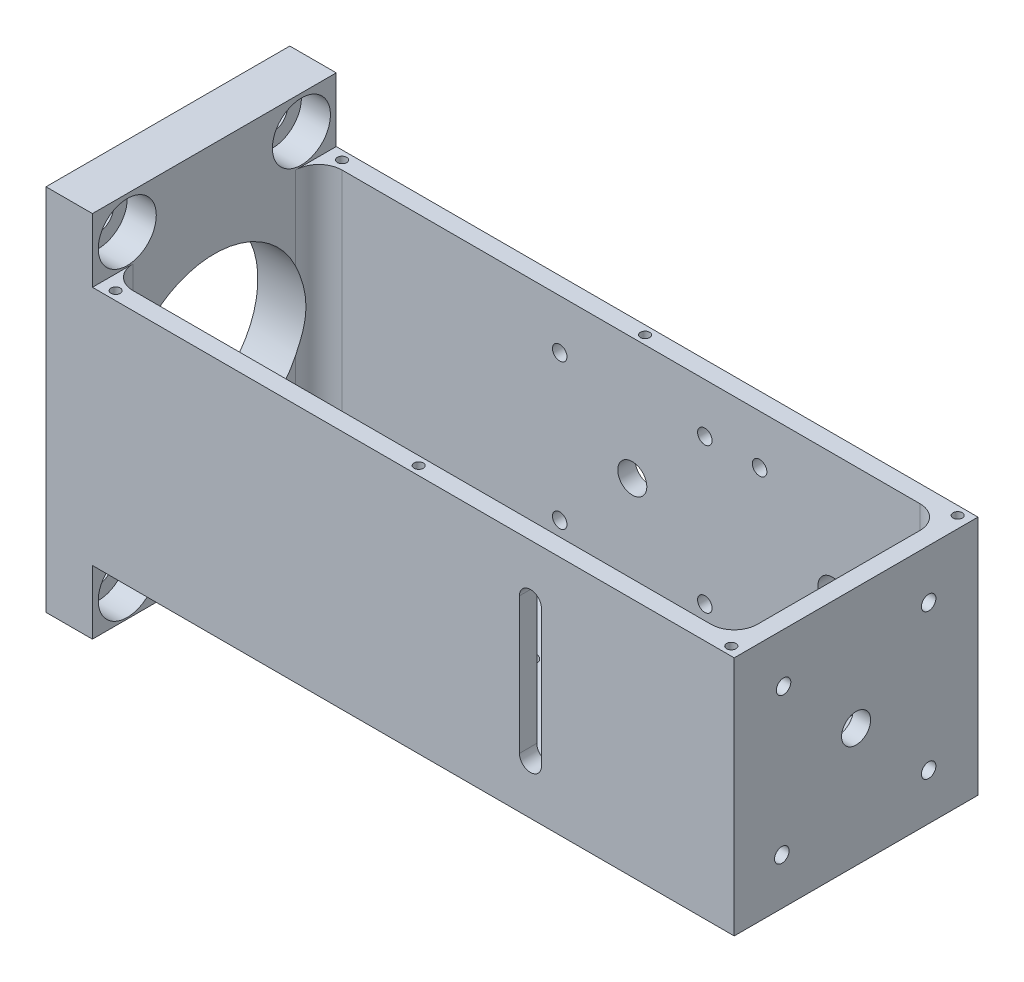
SolidWorks part; units mm, degrees
material "6061-T6 (SS)"
ref_plane "Front Plane" through (0, 0, 0) normal (0, 0, 1) x (1, 0, 0)
ref_plane "Top Plane" through (0, 0, 0) normal (0, 1, 0) x (1, 0, 0)
ref_plane "Right Plane" through (0, 0, 0) normal (1, 0, 0) x (0, 0, -1)
sketch "Sketch1" plane through (0, 0, 0) normal (0, 1, 0) x (1, 0, 0)
  line L1 (-59.28, -21) -> (59.28, -21)
  line L2 (-59.28, -21) -> (-59.28, 21)
  line L3 (-59.28, 21) -> (59.28, 21)
  line L4 (59.28, -21) -> (59.28, 21)
  line L5 (-59.28, -21) -> (59.28, 21) construction
  line L6 (-59.28, 21) -> (59.28, -21) construction
  point P0 (0, 0)
  dimension "D1" = 118.56
  dimension "D2" = 42
extrude "Boss-Extrude1" add sketch "Sketch1" along normal blind 41.5
sketch "Sketch2" plane through (0, 41.5, 0) normal (0, 1, 0) x (1, 0, 0)
  line L0 (59.28, -21) -> (59.28, 21) construction
  line L1 (56.28, -18) -> (-51.28, -18)
  line L2 (56.28, -18) -> (56.28, 18)
  line L3 (56.28, 18) -> (-51.28, 18)
  line L4 (-51.28, -18) -> (-51.28, 18)
  line L5 (-59.28, -21) -> (59.28, -21) construction
  line L6 (59.28, 21) -> (-59.28, 21) construction
  line L7 (-59.28, 21) -> (-59.28, -21) construction
  point P0 (0, 0)
  dimension "D1" = 3
  dimension "D2" = 3
  dimension "D3" = 3
  dimension "D4" = 8
extrude "Cut-Extrude1" cut sketch "Sketch2" against normal blind 37.5
fillet "Fillet1" radius 4 4 edges at (56.28, 22.75, -18) (-51.28, 22.75, -18) (56.28, 22.75, 18) (-51.28, 22.75, 18)
sketch "Sketch3" plane through (-59.28, 0, 0) normal (-1, 0, 0) x (0, 0, 1)
  line L0 (-21, 0) -> (21, 0) construction
  line L1 (21, 41.5) -> (21, 0) construction
  circle A0 centre (0, 20.5) radius 15.5
  dimension "D1" = 31
  dimension "D2" = 20.5
  dimension "D3" = 21
extrude "Cut-Extrude2" cut sketch "Sketch3" against normal up to next
sketch "Sketch10" plane through (0, 0, 21) normal (0, 0, 1) x (1, 0, 0)
  line L0 (24.18, 8.0181) -> (24.18, 32.9819) construction
  line L1 (-59.28, 0) -> (59.28, 0) construction
  line L3 (26.08, 32.25) -> (26.08, 8.75)
  line L5 (22.28, 32.25) -> (22.28, 8.75)
  line L8 (59.28, 41.5) -> (59.28, 0) construction
  arc A0 (22.28, 8.75) -> (26.08, 8.75) centre (24.18, 8.75) ccw
  arc A1 (26.08, 32.25) -> (22.28, 32.25) centre (24.18, 32.25) ccw
  point P2 (24.18, 20.5)
  dimension "D2" = 3.8
  dimension "D1" = 8.75
  dimension "D4" = 35.1
  dimension "D7" = 23.5
extrude "Cut-Extrude5" cut sketch "Sketch10" against normal up to next
sketch "Sketch22" plane through (0, 0, 0) normal (0, -1, 0) x (1, 0, 0)
  line L0 (59.28, -21) -> (-59.28, -21) construction
  line L1 (-51.28, -21) -> (-59.28, -21)
  line L2 (-51.28, -21) -> (-51.28, 21)
  line L3 (-51.28, 21) -> (-59.28, 21)
  line L4 (-59.28, -21) -> (-59.28, 21)
  line L5 (-51.28, -21) -> (-59.28, 21) construction
  line L6 (-51.28, 21) -> (-59.28, -21) construction
  point P4 (-55.28, 0)
extrude "Boss-Extrude3" add sketch "Sketch22" along normal blind 11
sketch "Sketch23" plane through (0, 41.5, 0) normal (0, 1, 0) x (1, 0, 0)
  line L1 (-51.28, -21) -> (-59.28, -21)
  line L2 (-51.28, -21) -> (-51.28, 21)
  line L3 (-51.28, 21) -> (-59.28, 21)
  line L4 (-59.28, -21) -> (-59.28, 21)
  line L5 (-51.28, -21) -> (-59.28, 21) construction
  line L6 (-51.28, 21) -> (-59.28, -21) construction
  point P4 (-55.28, 0)
extrude "Boss-Extrude4" add sketch "Sketch23" along normal blind 11
hole_wizard "Ø4.0mm Dowel Hole2" positions "Sketch26" profile "Sketch27" hole size "Ø4.0" standard "ANSI Metric"
sketch "Sketch26" plane through (-59.28, 0, 0) normal (-1, 0, 0) x (0, 0, 1)
  circle A0 centre (0, 20.5) radius 15.5 construction
  point P0 (0, 46.75)
  point P2 (0, -5.75)
  dimension "D2" = 26.25
  dimension "D1" = 52.5
sketch "Sketch27" plane through (-59.28, 46.75, 0) normal (0, 1, 0) x (0, 0, 1)
  line L0 (0, 0) -> (0, 5.7017)
  line L1 (0, 5.7017) -> (2, 4.5)
  line L2 (2, 4.5) -> (2, 0)
  line L5 (2, 0) -> (0, 0)
  line L10 (0, 5.7017) -> (-2, 4.5) construction
  line L11 (0, -6.35) -> (0, 107.95) construction
  dimension "Hole Dia." = 4
  dimension "Hole Depth" = 4.5
  dimension "Drill Angle" = 118
hole_wizard "CBORE for M5 SHCS1" positions "Sketch28" profile "Sketch29" counterbore size "M5" standard "ANSI Metric" end condition through all
sketch "Sketch28" plane through (-51.28, 0, 0) normal (1, 0, 0) x (0, 0, -1)
  arc A0 (14, 27.1521) -> (-14, 27.1521) centre (0, 20.5) ccw construction
  point P0 (-15, 46.75)
  point P2 (15, 46.75)
  point P4 (-15, -5.75)
  point P6 (15, -5.75)
  dimension "D1" = 52.5
  dimension "D2" = 30
  dimension "D3" = 15
  dimension "D4" = 26.25
sketch "Sketch29" plane through (-51.28, 46.75, 15) normal (0, 1, 0) x (0, 0, -1)
  line L0 (0, 0) -> (0, 8)
  line L1 (0, 8) -> (2.65, 8)
  line L3 (2.65, 8) -> (2.65, 5)
  line L4 (2.65, 5) -> (5, 5)
  line L5 (5, 5) -> (5, 0)
  line L7 (5, 0) -> (0, 0)
  line L11 (0, -6.35) -> (0, 107.95) construction
  dimension "Thru Hole Dia." = 5.3
  dimension "Thru Hole Depth" = 8
  dimension "C'Bore Dia." = 10
  dimension "C'Bore Depth" = 5
hole_wizard "Ø5.0mm Dowel Hole1" positions "Sketch30" profile "Sketch31" hole size "Ø5.0" standard "ANSI Metric" end condition up to next
sketch "Sketch30" plane through (0, 0, -21) normal (0, 0, -1) x (-1, 0, 0)
  point P0 (-2.7215, 20.5)
  point P4 (-37.2075, 20.5)
sketch "Sketch31" plane through (2.7215, 20.5, -21) normal (1, 0, 0) x (0, 1, 0)
  line L0 (0, 0) -> (0, 3)
  line L1 (0, 3) -> (2.5, 3)
  line L2 (2.5, 3) -> (2.5, 0)
  line L5 (2.5, 0) -> (0, 0)
  line L11 (0, -6.35) -> (0, 107.95) construction
  dimension "Thru Hole Dia." = 5
  dimension "Thru Hole Depth" = 3
hole_wizard "Ø5.0mm Dowel Hole2" positions "Sketch32" profile "Sketch33" hole size "Ø5.0" standard "ANSI Metric" end condition up to next
sketch "Sketch32" plane through (59.28, 0, 0) normal (1, 0, 0) x (0, 0, -1)
  point P0 (0, 20.5)
sketch "Sketch33" plane through (59.28, 20.5, 0) normal (0, 1, 0) x (0, 0, -1)
  line L0 (0, 0) -> (0, 3)
  line L1 (0, 3) -> (2.5, 3)
  line L2 (2.5, 3) -> (2.5, 0)
  line L5 (2.5, 0) -> (0, 0)
  line L11 (0, -6.35) -> (0, 107.95) construction
  dimension "Thru Hole Dia." = 5
  dimension "Thru Hole Depth" = 3
hole_wizard "M3x0.5 Tapped Hole1" positions "Sketch34" profile "Sketch35" tap size "M3x0.5" standard "ANSI Metric" end condition up to next
sketch "Sketch34" plane through (0, 0, -21) normal (0, 0, -1) x (-1, 0, 0)
  point P0 (9.7785, 8)
  point P3 (-15.2215, 8)
  point P6 (-15.2215, 33)
  point P9 (9.7785, 33)
  point P12 (-24.6564, 7.9489)
  point P15 (-49.7587, 7.9489)
  point P18 (-49.7587, 33.0511)
  point P21 (-24.6564, 33.0511)
sketch "Sketch35" plane through (-9.7785, 8, -21) normal (1, 0, 0) x (0, 1, 0)
  line L0 (0, 0) -> (0, 3)
  line L1 (0, 3) -> (1.25, 3)
  line L2 (1.25, 3) -> (1.25, 0)
  line L5 (1.25, 0) -> (0, 0)
  line L11 (0, -6.35) -> (0, 107.95) construction
  dimension "Thru Tap Drill Dia." = 2.5
  dimension "Thru Tap Drill Depth" = 3
cosmetic thread "Hole Thread1" parameters "D2"=3
cosmetic thread "Hole Thread2" parameters "D2"=3
cosmetic thread "Hole Thread3" parameters "D2"=3
cosmetic thread "Hole Thread4" parameters "D2"=3
cosmetic thread "Hole Thread5" parameters "D2"=3
cosmetic thread "Hole Thread6" parameters "D2"=3
cosmetic thread "Hole Thread7" parameters "D2"=3
cosmetic thread "Hole Thread8" parameters "D2"=3
hole_wizard "M3x0.5 Tapped Hole2" positions "Sketch36" profile "Sketch37" tap size "M3x0.5" standard "ANSI Metric" end condition up to next
sketch "Sketch36" plane through (59.28, 0, 0) normal (1, 0, 0) x (0, 0, -1)
  ellipse E0 centre (-11.738, 8) end of major axis (-11.738, 6.5) minor radius 1.0607 (-11.738, 9.5) -> (-10.6773, 8) ccw construction
  point P0 (12.5, 8)
  point P3 (-12.7986, 8)
  point P12 (-12.5, 33)
  point P15 (12.5, 33)
sketch "Sketch37" plane through (59.28, 8, -12.5) normal (0, 1, 0) x (0, 0, -1)
  line L0 (0, 0) -> (0, 3)
  line L1 (0, 3) -> (1.25, 3)
  line L2 (1.25, 3) -> (1.25, 0)
  line L5 (1.25, 0) -> (0, 0)
  line L11 (0, -6.35) -> (0, 107.95) construction
  dimension "Thru Tap Drill Dia." = 2.5
  dimension "Thru Tap Drill Depth" = 3
cosmetic thread "Hole Thread9" parameters "D2"=3
cosmetic thread "Hole Thread10" parameters "D2"=3
cosmetic thread "Hole Thread11" parameters "D2"=3
cosmetic thread "Hole Thread12" parameters "D2"=3
hole_wizard "Ø3.0mm Dowel Hole1" positions "Sketch38" profile "Sketch39" hole size "Ø3.0" standard "ANSI Metric"
sketch "Sketch38" plane through (0, 4, 0) normal (0, 1, 0) x (1, 0, 0)
  point P0 (-4.7031, -10.253)
  point P3 (12.9746, 7.4246)
sketch "Sketch39" plane through (-4.7031, 4, 10.253) normal (1, 0, 0) x (0, 0, 1)
  line L0 (0, 0) -> (0, 3.9013)
  line L1 (0, 3.9013) -> (1.5, 3)
  line L2 (1.5, 3) -> (1.5, 0)
  line L5 (1.5, 0) -> (0, 0)
  line L10 (0, 3.9013) -> (-1.5, 3) construction
  line L11 (0, -6.35) -> (0, 107.95) construction
  dimension "Hole Dia." = 3
  dimension "Hole Depth" = 3
  dimension "Drill Angle" = 118
hole_wizard "CBORE for M2.5 SHCS1" positions "Sketch42" profile "Sketch43" counterbore size "M2.5" standard "ANSI Metric" end condition up to next
sketch "Sketch42" plane through (0, 0, 0) normal (0, -1, 0) x (-1, 0, 0)
  point P0 (-4.1701, -1.4486)
sketch "Sketch43" plane through (4.1701, 0, 1.4486) normal (1, 0, 0) x (0, 0, -1)
  line L0 (0, 0) -> (0, 4)
  line L1 (0, 4) -> (1.45, 4)
  line L3 (1.45, 4) -> (1.45, 2.5)
  line L4 (1.45, 2.5) -> (2.75, 2.5)
  line L5 (2.75, 2.5) -> (2.75, 0)
  line L7 (2.75, 0) -> (0, 0)
  line L11 (0, -6.35) -> (0, 107.95) construction
  dimension "Thru Hole Dia." = 2.9
  dimension "Thru Hole Depth" = 4
  dimension "C'Bore Dia." = 5.5
  dimension "C'Bore Depth" = 2.5
hole_wizard "1/16 (0.0625) Dowel Hole1" positions "Sketch44" profile "Sketch45" hole size "1/16" standard "ANSI Inch"
sketch "Sketch44" plane through (0, 4, 0) normal (0, 1, 0) x (1, 0, 0)
  point P0 (41.0862, -3.8787)
  point P3 (33.3289, 3.8787)
sketch "Sketch45" plane through (41.0862, 4, 3.8787) normal (1, 0, 0) x (0, 0, 1)
  line L0 (0, 0) -> (0, 3.4769)
  line L1 (0, 3.4769) -> (0.7937, 3)
  line L2 (0.7937, 3) -> (0.7937, 0)
  line L5 (0.7937, 0) -> (0, 0)
  line L10 (0, 3.4769) -> (-0.7938, 3) construction
  line L11 (0, -6.35) -> (0, 107.95) construction
  dimension "Hole Dia." = 1.5875
  dimension "Hole Depth" = 3
  dimension "Drill Angle" = 118
hole_wizard "CBORE for M2 SHCS1" positions "Sketch46" profile "Sketch47" counterbore size "M2" standard "ANSI Metric" end condition up to next
sketch "Sketch46" plane through (0, 0, 0) normal (0, -1, 0) x (-1, 0, 0)
  point P0 (-41.0862, 3.8787)
  point P3 (-33.3289, -3.8787)
sketch "Sketch47" plane through (41.0862, 0, -3.8787) normal (1, 0, 0) x (0, 0, -1)
  line L0 (0, 0) -> (0, 4)
  line L1 (0, 4) -> (1.1, 4)
  line L3 (1.1, 4) -> (1.1, 2)
  line L4 (1.1, 2) -> (2.2, 2)
  line L5 (2.2, 2) -> (2.2, 0)
  line L7 (2.2, 0) -> (0, 0)
  line L11 (0, -6.35) -> (0, 107.95) construction
  dimension "Thru Hole Dia." = 2.2
  dimension "Thru Hole Depth" = 4
  dimension "C'Bore Dia." = 4.4
  dimension "C'Bore Depth" = 2
hole_wizard "Ø3.0mm Dowel Hole2" positions "Sketch48" profile "Sketch49" hole size "Ø3.0" standard "ANSI Metric"
sketch "Sketch48" plane through (0, 4, 0) normal (0, 1, 0) x (1, 0, 0)
  point P0 (23.8944, -11.8366)
  point P3 (23.1266, 10.15)
sketch "Sketch49" plane through (23.8944, 4, 11.8366) normal (1, 0, 0) x (0, 0, 1)
  line L0 (0, 0) -> (0, 3.9013)
  line L1 (0, 3.9013) -> (1.5, 3)
  line L2 (1.5, 3) -> (1.5, 0)
  line L5 (1.5, 0) -> (0, 0)
  line L10 (0, 3.9013) -> (-1.5, 3) construction
  line L11 (0, -6.35) -> (0, 107.95) construction
  dimension "Hole Dia." = 3
  dimension "Hole Depth" = 3
  dimension "Drill Angle" = 118
hole_wizard "CBORE for M2.5 SHCS2" positions "Sketch50" profile "Sketch51" counterbore size "M2.5" standard "ANSI Metric" end condition up to next
sketch "Sketch50" plane through (0, 0, 0) normal (0, -1, 0) x (-1, 0, 0)
  point P0 (-23.4582, 0.6557)
sketch "Sketch51" plane through (23.4582, 0, -0.6557) normal (1, 0, 0) x (0, 0, -1)
  line L0 (0, 0) -> (0, 4)
  line L1 (0, 4) -> (1.45, 4)
  line L3 (1.45, 4) -> (1.45, 2.5)
  line L4 (1.45, 2.5) -> (2.75, 2.5)
  line L5 (2.75, 2.5) -> (2.75, 0)
  line L7 (2.75, 0) -> (0, 0)
  line L11 (0, -6.35) -> (0, 107.95) construction
  dimension "Thru Hole Dia." = 2.9
  dimension "Thru Hole Depth" = 4
  dimension "C'Bore Dia." = 5.5
  dimension "C'Bore Depth" = 2.5
hole_wizard "M2x0.4 Tapped Hole1" positions "Sketch52" profile "Sketch53" tap size "M2x0.4" standard "ANSI Metric"
sketch "Sketch52" plane through (0, 41.5, 0) normal (0, 1, 0) x (1, 0, 0)
  point P0 (57.28, -19.5)
  point P3 (3.4205, -19.5)
  point P6 (-48.78, -19.5)
  point P9 (-48.78, 19.5)
  point P12 (3.4205, 19.5)
  point P15 (57.28, 19.5)
sketch "Sketch53" plane through (57.28, 41.5, 19.5) normal (1, 0, 0) x (0, 0, 1)
  line L0 (0, 0) -> (0, 5.6807)
  line L1 (0, 5.6807) -> (0.8, 5.2)
  line L2 (0.8, 5.2) -> (0.8, 0)
  line L5 (0.8, 0) -> (0, 0)
  line L10 (0, 5.6807) -> (-0.8, 5.2) construction
  line L11 (0, -6.35) -> (0, 107.95) construction
  dimension "Tap Drill Dia." = 1.6
  dimension "Tap Drill Depth" = 5.2
  dimension "Drill Angle" = 118
cosmetic thread "Hole Thread13" parameters "D1"=4, "D2"=2
cosmetic thread "Hole Thread14" parameters "D1"=4, "D2"=2
cosmetic thread "Hole Thread15" parameters "D1"=4, "D2"=2
cosmetic thread "Hole Thread16" parameters "D1"=4, "D2"=2
cosmetic thread "Hole Thread17" parameters "D1"=4, "D2"=2
cosmetic thread "Hole Thread18" parameters "D1"=4, "D2"=2
